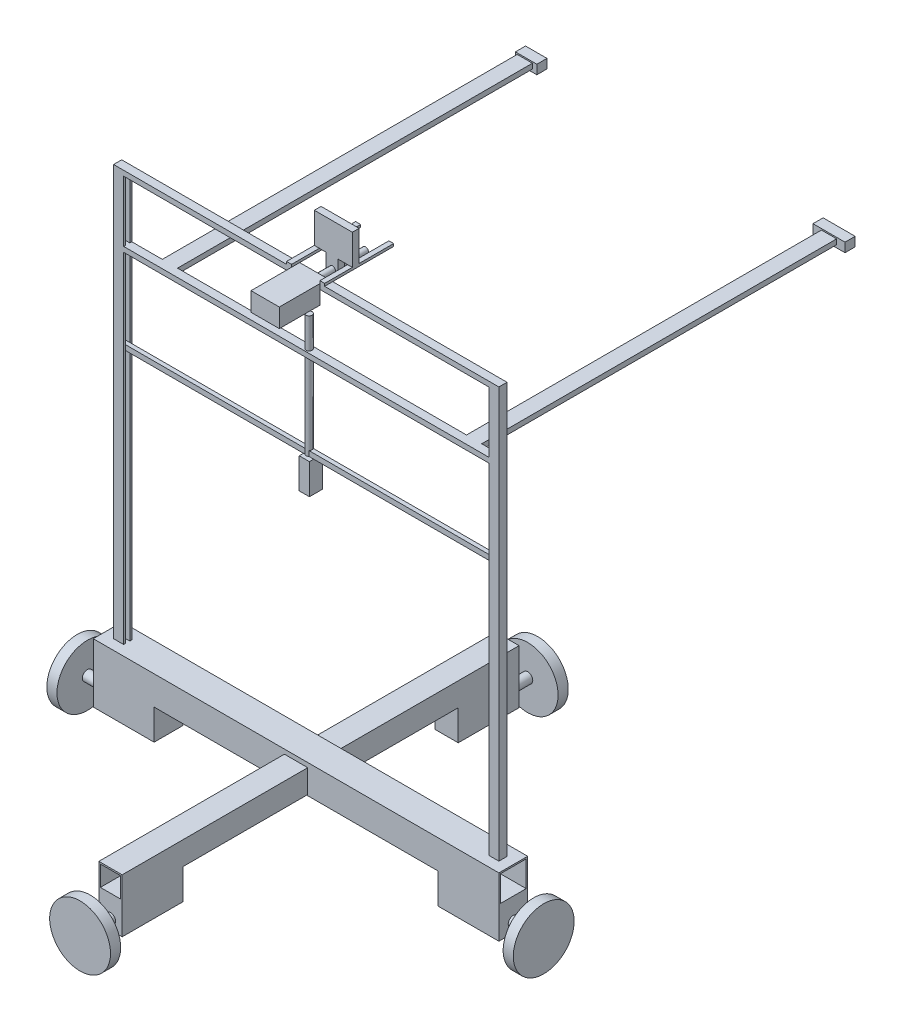
SolidWorks part; units mm, degrees
ref_plane "Front Plane" through (0, 0, 0) normal (0, 0, 1) x (1, 0, 0)
ref_plane "Top Plane" through (0, 0, 0) normal (0, 1, 0) x (1, 0, 0)
ref_plane "Right Plane" through (0, 0, 0) normal (1, 0, 0) x (0, 0, -1)
sketch "Sketch1" plane through (0, 0, 0) normal (1, 0, 0) x (0, 0, -1)
  line L1 (12.7, -12.7) -> (-12.7, -12.7)
  line L2 (12.7, -12.7) -> (12.7, 12.7)
  line L3 (12.7, 12.7) -> (-12.7, 12.7)
  line L4 (-12.7, -12.7) -> (-12.7, 12.7)
  line L5 (12.7, -12.7) -> (-12.7, 12.7) construction
  line L6 (12.7, 12.7) -> (-12.7, -12.7) construction
  point P0 (0, 0)
  dimension "D1" = 25.4
  dimension "D2" = 25.4
extrude "Extrude-Thin1" add sketch "Sketch1" along normal blind 400 thin contours L3 L4 L1 L2 thin type one direction wall 1.5
sketch "Sketch2" plane through (0, 0, 14.2) normal (0, 0, 1) x (1, 0, 0)
  line L0 (0, -14.2) -> (0, 14.2) construction
  line L1 (210, -11.6936) -> (190, -11.6936)
  line L2 (210, -11.6936) -> (210, 8.3064)
  line L3 (210, 8.3064) -> (190, 8.3064)
  line L4 (190, -11.6936) -> (190, 8.3064)
  line L5 (210, -11.6936) -> (190, 8.3064) construction
  line L6 (210, 8.3064) -> (190, -11.6936) construction
  point P0 (200, -1.6936)
  dimension "D1" = 20
  dimension "D2" = 20
  dimension "D3" = 200
extrude "Extrude-Thin2" add sketch "Sketch2" along normal blind 183 and the other way blind 208.4 thin thin type one direction wall 1.5
sketch "Sketch3" plane through (0, -14.2, 0) normal (0, -1, 0) x (-1, 0, 0)
  line L0 (-400, 14.2) -> (0, 14.2) construction
  line L1 (-400, -14.2) -> (-340, -14.2)
  line L2 (-400, -14.2) -> (-400, 14.2)
  line L3 (-400, 14.2) -> (-340, 14.2)
  line L4 (-340, -14.2) -> (-340, 14.2)
  line L6 (0, -14.2) -> (-60, -14.2)
  line L7 (0, -14.2) -> (0, 14.2)
  line L8 (0, 14.2) -> (-60, 14.2)
  line L9 (-60, -14.2) -> (-60, 14.2)
  dimension "D1" = 60
  dimension "D2" = 28.4
  dimension "D3" = 60
extrude "Boss-Extrude1" add sketch "Sketch3" along normal blind 30
sketch "Sketch4" plane through (0, -13.1936, 0) normal (0, -1, 0) x (-1, 0, 0)
  line L0 (-188.5, -14.2) -> (-188.5, -197.2) construction
  line L1 (-211.5, -197.2) -> (-188.5, -197.2)
  line L2 (-211.5, -197.2) -> (-211.5, -137.2)
  line L3 (-211.5, -137.2) -> (-188.5, -137.2)
  line L4 (-188.5, -197.2) -> (-188.5, -137.2)
  line L5 (-188.5, 194.2) -> (-188.5, 14.2) construction
  line L6 (-211.5, 194.2) -> (-188.5, 194.2)
  line L7 (-211.5, 194.2) -> (-211.5, 134.2)
  line L8 (-211.5, 134.2) -> (-188.5, 134.2)
  line L9 (-188.5, 194.2) -> (-188.5, 134.2)
  dimension "D1" = 60
extrude "Boss-Extrude2" add sketch "Sketch4" along normal blind 30
sketch "Sketch5" plane through (400, 0, 0) normal (1, 0, 0) x (0, 0, -1)
  line L0 (14.2, -44.2) -> (-14.2, -44.2) construction
  circle A0 centre (0, -34.2) radius 5
  dimension "D1" = 10
extrude "Boss-Extrude3" add sketch "Sketch5" along normal blind 30
sketch "Sketch6" plane through (0, 0, -194.2) normal (0, 0, -1) x (-1, 0, 0)
  line L0 (-188.5, -43.1936) -> (-211.5, -43.1936) construction
  circle A0 centre (-200, -33.1936) radius 5
  dimension "D1" = 10
extrude "Boss-Extrude4" add sketch "Sketch6" along normal blind 30
sketch "Sketch7" plane through (0, 0, 0) normal (-1, 0, 0) x (0, 0, 1)
  line L0 (14.2, -44.2) -> (-14.2, -44.2) construction
  circle A0 centre (0, -34.2) radius 5
  dimension "D1" = 10
extrude "Boss-Extrude5" add sketch "Sketch7" along normal blind 30
sketch "Sketch8" plane through (0, 0, 197.2) normal (0, 0, 1) x (1, 0, 0)
  line L0 (211.5, -43.1936) -> (188.5, -43.1936) construction
  circle A0 centre (200, -33.1936) radius 5
  dimension "D1" = 10
extrude "Boss-Extrude6" add sketch "Sketch8" along normal blind 30
sketch "Sketch9" plane through (0, 14.2, 0) normal (0, 1, 0) x (1, 0, 0)
  line L0 (10, 3.8) -> (20, 3.8)
  line L1 (20, -2.2) -> (20, -4.2)
  line L2 (10, 3.8) -> (10, -4.2)
  line L3 (10, -4.2) -> (20, -4.2)
  line L4 (20, 3.8) -> (20, 1.8)
  line L5 (0, 14.2) -> (0, -14.2) construction
  line L6 (20, 1.8) -> (13.1775, 1.8)
  line L7 (400, 14.2) -> (400, -14.2) construction
  line L8 (20, -2.2) -> (13.1775, -2.2)
  line L9 (13.1775, 1.8) -> (13.1775, -2.2)
  line L10 (380, 3.8) -> (390, 3.8)
  line L11 (380, 3.8) -> (380, 1.8)
  line L12 (380, -4.2) -> (390, -4.2)
  line L13 (390, 3.8) -> (390, -4.2)
  line L14 (400, -14.2) -> (0, -14.2) construction
  line L15 (380, -2.2) -> (380, -4.2)
  line L16 (380, 1.8) -> (385.5268, 1.8)
  line L18 (380, -2.2) -> (385.5268, -2.2)
  line L19 (385.5268, 1.8) -> (385.5268, -2.2)
  dimension "D1" = 10
  dimension "D2" = 10
  dimension "D3" = 4
  dimension "D4" = 2
  dimension "D5" = 10
  dimension "D6" = 10
  dimension "D7" = 8
  dimension "D8" = 10
  dimension "D9" = 2
  dimension "D10" = 10
  dimension "D11" = 4
  dimension "D12" = 2
extrude "Boss-Extrude7" add sketch "Sketch9" along normal blind 400
ref_plane "Plane1" through (0, 264.2, 0) normal (0, 1, 0) x (1, 0, 0)
sketch "Sketch10" plane through (0, 264.2, 0) normal (0, 1, 0) x (1, 0, 0)
  line L0 (385.5268, 1.8) -> (385.5268, -2.2) construction
  line L1 (13.1775, -2.2) -> (385.5268, -2.2)
  line L2 (13.1775, -2.2) -> (13.1775, 1.8)
  line L3 (13.1775, 1.8) -> (385.5268, 1.8)
  line L4 (385.5268, -2.2) -> (385.5268, 1.8)
  line L5 (385.5268, 1.8) -> (385.5268, -2.2) construction
extrude "Boss-Extrude8" add sketch "Sketch10" along normal blind 5
sketch "Sketch11" plane through (0, 414.2, 0) normal (0, 1, 0) x (1, 0, 0)
  line L1 (10, 3.8) -> (390, 3.8)
  line L2 (10, 3.8) -> (10, -4.2)
  line L3 (10, -4.2) -> (390, -4.2)
  line L4 (390, 3.8) -> (390, -4.2)
extrude "Boss-Extrude9" add sketch "Sketch11" along normal blind 5
sketch "Sketch12" plane through (0, 0, 4.2) normal (0, 0, 1) x (1, 0, 0)
  line L0 (10, 419.2) -> (390, 419.2) construction
  line L1 (185.5611, 419.2) -> (213.4763, 419.2)
  line L2 (185.5611, 419.2) -> (185.5611, 400.7148)
  line L3 (185.5611, 400.7148) -> (213.4763, 400.7148)
  line L4 (213.4763, 419.2) -> (213.4763, 400.7148)
extrude "Boss-Extrude10" add sketch "Sketch12" along normal blind 40 contours L3 L4 L1 L2
sketch "Sketch13" plane through (0, 0, 4.2) normal (0, 0, -1) x (-1, 0, 0)
  circle A0 centre (-198.4907, 410.1673) radius 3
extrude "Boss-Extrude11" add sketch "Sketch13" along normal blind 60
sketch "Sketch14" plane through (0, 419.2, 0) normal (0, 1, 0) x (1, 0, 0)
  line L1 (213.4763, -4.2) -> (218.1317, -4.2)
  line L2 (213.4763, -4.2) -> (213.4763, 63.8753)
  line L3 (213.4763, 63.8753) -> (218.1317, 63.8753)
  line L4 (218.1317, -4.2) -> (218.1317, 63.8753)
  line L5 (185.5611, -4.2) -> (180.5841, -4.2)
  line L6 (185.5611, -4.2) -> (185.5611, 63.8753)
  line L7 (185.5611, 63.8753) -> (180.5841, 63.8753)
  line L8 (180.5841, -4.2) -> (180.5841, 63.8753)
extrude "Boss-Extrude12" add sketch "Sketch14" along normal blind 2.5
sketch "Sketch15" plane through (0, 421.7, 0) normal (0, 1, 0) x (1, 0, 0)
  line L0 (180.5841, 63.8753) -> (180.5841, -4.2) construction
  line L1 (180.5841, 23.1842) -> (218.1317, 23.1842)
  line L2 (180.5841, 23.1842) -> (180.5841, 29.8377)
  line L3 (180.5841, 29.8377) -> (218.1317, 29.8377)
  line L4 (218.1317, 23.1842) -> (218.1317, 29.8377)
  line L5 (218.1317, -4.2) -> (218.1317, 63.8753) construction
extrude "Boss-Extrude13" add sketch "Sketch15" along normal blind 30
sketch "Sketch16" plane through (0, 421.7, 0) normal (0, -1, 0) x (-1, 0, 0)
  line L0 (-213.4763, 29.8377) -> (-185.5611, 29.8377) construction
  line L1 (-203.8256, 29.8377) -> (-192.2933, 29.8377)
  line L2 (-203.8256, 29.8377) -> (-203.8256, 23.1842)
  line L3 (-203.8256, 23.1842) -> (-192.2933, 23.1842)
  line L4 (-192.2933, 29.8377) -> (-192.2933, 23.1842)
  line L5 (-185.5611, 23.1842) -> (-213.4763, 23.1842) construction
extrude "Boss-Extrude14" add sketch "Sketch16" along normal blind 16
sketch "Sketch17" plane through (0, 264.2, 0) normal (0, -1, 0) x (-1, 0, 0)
  line L1 (-205.3829, 6.4313) -> (-195.3288, 6.4313)
  line L2 (-205.3829, 6.4313) -> (-205.3829, -6.4313)
  line L3 (-205.3829, -6.4313) -> (-195.3288, -6.4313)
  line L4 (-195.3288, 6.4313) -> (-195.3288, -6.4313)
  line L5 (-205.3829, 6.4313) -> (-195.3288, -6.4313) construction
  line L6 (-205.3829, -6.4313) -> (-195.3288, 6.4313) construction
  point P0 (-200.3558, 0)
extrude "Boss-Extrude15" add sketch "Sketch17" along normal blind 30
sketch "Sketch18" plane through (0, 264.2, 0) normal (0, 1, 0) x (1, 0, 0)
  circle A0 centre (198.6047, 0) radius 3
extrude "Boss-Extrude16" add sketch "Sketch18" along normal blind 120
ref_plane "Plane2" through (0, 349.2, 0) normal (0, 1, 0) x (1, 0, 0)
sketch "Sketch19" plane through (0, 349.2, 0) normal (0, 1, 0) x (1, 0, 0)
  line L1 (390, 3.8) -> (10, 3.8)
  line L2 (390, 3.8) -> (390, -4.2)
  line L3 (390, -4.2) -> (10, -4.2)
  line L4 (10, 3.8) -> (10, -4.2)
extrude "Boss-Extrude17" add sketch "Sketch19" along normal blind 5 contours L1 L4 L3 L2
sketch "Sketch22" plane through (0, 0, -3.8) normal (0, 0, -1) x (-1, 0, 0)
  line L0 (-380, 349.2) -> (-20, 349.2) construction
  line L1 (-365.0617, 349.2) -> (-350.0617, 349.2)
  line L2 (-365.0617, 349.2) -> (-365.0617, 354.2)
  line L3 (-365.0617, 354.2) -> (-350.0617, 354.2)
  line L4 (-350.0617, 349.2) -> (-350.0617, 354.2)
  line L5 (-380, 354.2) -> (-20, 354.2) construction
  line L7 (-50.0617, 349.2) -> (-65.0617, 349.2)
  line L8 (-50.0617, 349.2) -> (-50.0617, 354.2)
  line L9 (-50.0617, 354.2) -> (-65.0617, 354.2)
  line L10 (-65.0617, 349.2) -> (-65.0617, 354.2)
  dimension "D1" = 300
  dimension "D2" = 15
  dimension "D3" = 15
extrude "Boss-Extrude18" add sketch "Sketch22" along normal blind 350
sketch "Sketch23" plane through (0, 0, -353.8) normal (0, 0, -1) x (-1, 0, 0)
  line L1 (-69.4129, 355.5172) -> (-48.2838, 355.5172)
  line L2 (-69.4129, 355.5172) -> (-69.4129, 346.4727)
  line L3 (-69.4129, 346.4727) -> (-48.2838, 346.4727)
  line L4 (-48.2838, 355.5172) -> (-48.2838, 346.4727)
  line L5 (-373.341, 355.5172) -> (-341.7613, 355.5172)
  line L6 (-373.341, 355.5172) -> (-373.341, 346.4727)
  line L7 (-373.341, 346.4727) -> (-341.7613, 346.4727)
  line L8 (-341.7613, 355.5172) -> (-341.7613, 346.4727)
extrude "Boss-Extrude19" add sketch "Sketch23" along normal blind 10
sketch "Sketch24" plane through (0, 0, -224.2) normal (0, 0, -1) x (-1, 0, 0)
  circle A0 centre (-200, -33.1936) radius 30
extrude "Boss-Extrude20" add sketch "Sketch24" against normal blind 10
sketch "Sketch25" plane through (-30, 0, 0) normal (-1, 0, 0) x (0, 0, 1)
  circle A0 centre (0, -34.2) radius 30
extrude "Boss-Extrude21" add sketch "Sketch25" against normal blind 10
sketch "Sketch26" plane through (0, 0, 227.2) normal (0, 0, 1) x (1, 0, 0)
  circle A0 centre (200, -33.1936) radius 30
extrude "Boss-Extrude22" add sketch "Sketch26" against normal blind 10
sketch "Sketch27" plane through (430, 0, 0) normal (1, 0, 0) x (0, 0, -1)
  circle A0 centre (0, -34.2) radius 30
extrude "Boss-Extrude23" add sketch "Sketch27" against normal blind 10
